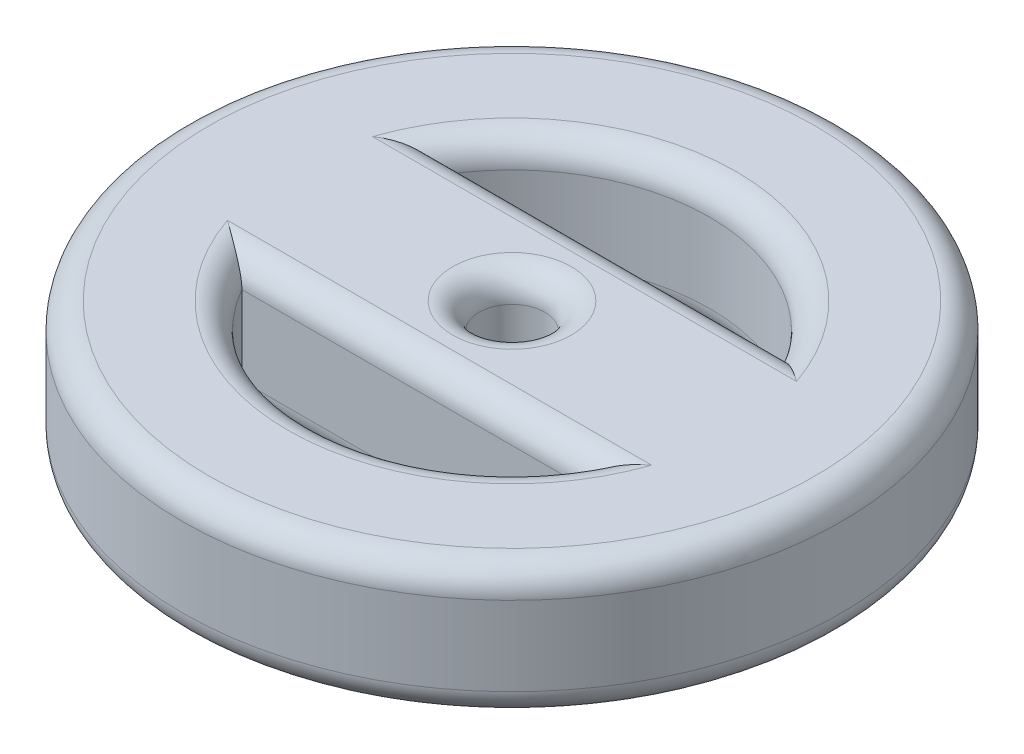
SolidWorks part; units mm, degrees
ref_plane "Face" through (0, 0, 0) normal (0, 0, 1) x (1, 0, 0)
ref_plane "Dessus" through (0, 0, 0) normal (0, 1, 0) x (1, 0, 0)
ref_plane "Droite" through (0, 0, 0) normal (1, 0, 0) x (0, 0, -1)
sketch "Esquisse1" plane through (0, 0, 0) normal (0, 1, 0) x (1, 0, 0)
  line L0 (0, 50) -> (0, -50) construction
  line L1 (-50, 0) -> (50, 0) construction
  line L2 (-25.9808, 15) -> (25.9808, 15)
  line L3 (-25.9808, -15) -> (25.9808, -15)
  circle A0 centre (0, 0) radius 50
  arc A1 (-25.9808, 15) -> (25.9808, 15) centre (0, 0) cw
  arc A2 (-25.9808, -15) -> (25.9808, -15) centre (0, 0) ccw
  circle A3 centre (0, 0) radius 5
  dimension "D1" = 100
  dimension "D2" = 30
  dimension "D4" = 10
  dimension "D3" = 15
extrude "Extrusion1" add sketch "Esquisse1" along normal blind 20
fillet "Congé1" radius 4 12 edges at (0, 0, -15) (0, 0, -30) (0, 0, 5) (0, 0, 30) (0, 0, 15) (0, 20, -30) (0, 20, -15) (0, 20, 5) (0, 20, 15) (0, 20, 30) (0, 0, 50) (0, 20, 50)
